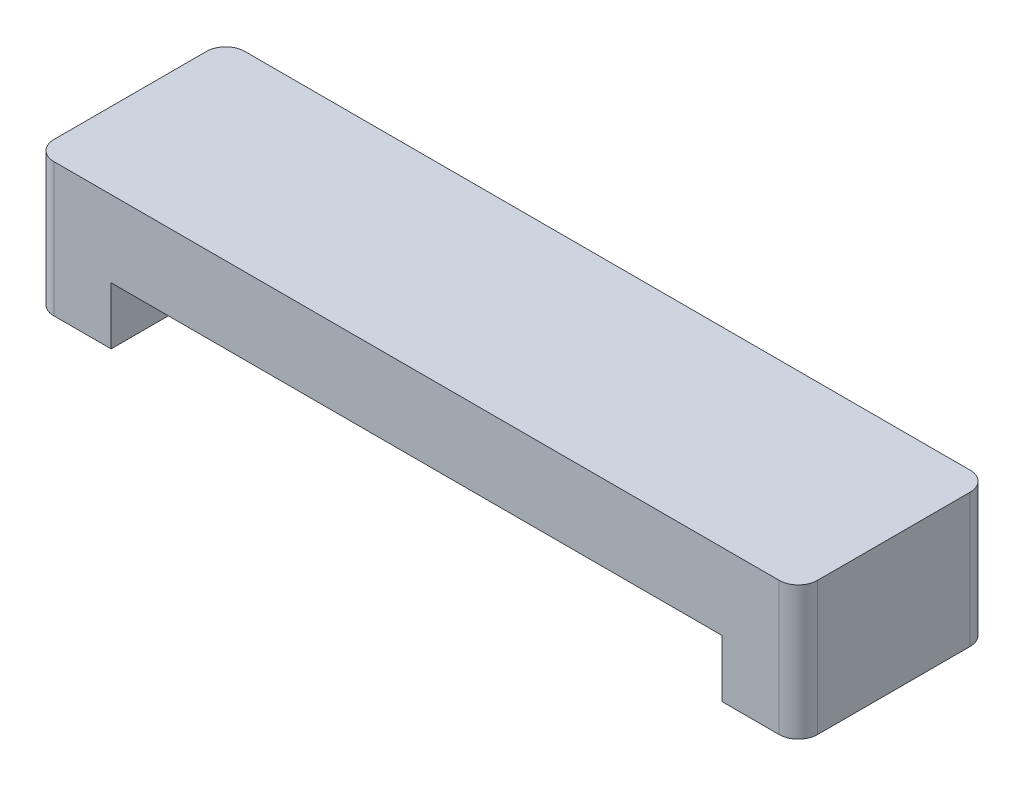
SolidWorks part; units mm, degrees
ref_plane "Ön Düzlem" through (0, 0, 0) normal (0, 0, 1) x (1, 0, 0)
ref_plane "Üst Düzlem" through (0, 0, 0) normal (0, 1, 0) x (1, 0, 0)
ref_plane "Sağ Düzlem" through (0, 0, 0) normal (1, 0, 0) x (0, 0, -1)
sketch "Çizim1" plane through (0, 0, 0) normal (0, 0, 1) x (1, 0, 0)
  line L1 (-51.4443, 55.5056) -> (28.5557, 55.5056)
  line L2 (-51.4443, 55.5056) -> (-51.4443, 41.5056)
  line L3 (-51.4443, 41.5056) -> (28.5557, 41.5056)
  line L4 (28.5557, 55.5056) -> (28.5557, 41.5056)
  dimension "D1" = 80
  dimension "D2" = 14
extrude "Yükseklik-Ekstrüzyon1" add sketch "Çizim1" along normal blind 20
sketch "Çizim2" plane through (0, 0, 20) normal (0, 0, 1) x (1, 0, 0)
  line L0 (-11.4443, 41.5056) -> (-43.4443, 41.5056)
  line L1 (-51.4443, 41.5056) -> (28.5557, 41.5056) construction
  line L2 (-43.4443, 41.5056) -> (-43.4443, 47.5056)
  line L3 (-43.4443, 47.5056) -> (20.5557, 47.5056)
  line L4 (20.5557, 47.5056) -> (20.5557, 41.5056)
  line L5 (20.5557, 41.5056) -> (-11.4443, 41.5056)
extrude "Kes-Ekstrüzyon1" cut sketch "Çizim2" against normal blind 8
fillet "Radyus1" radius 2 4 edges at (28.5557, 48.5056, 0) (28.5557, 48.5056, 20) (-51.4443, 48.5056, 0) (-51.4443, 48.5056, 20)
